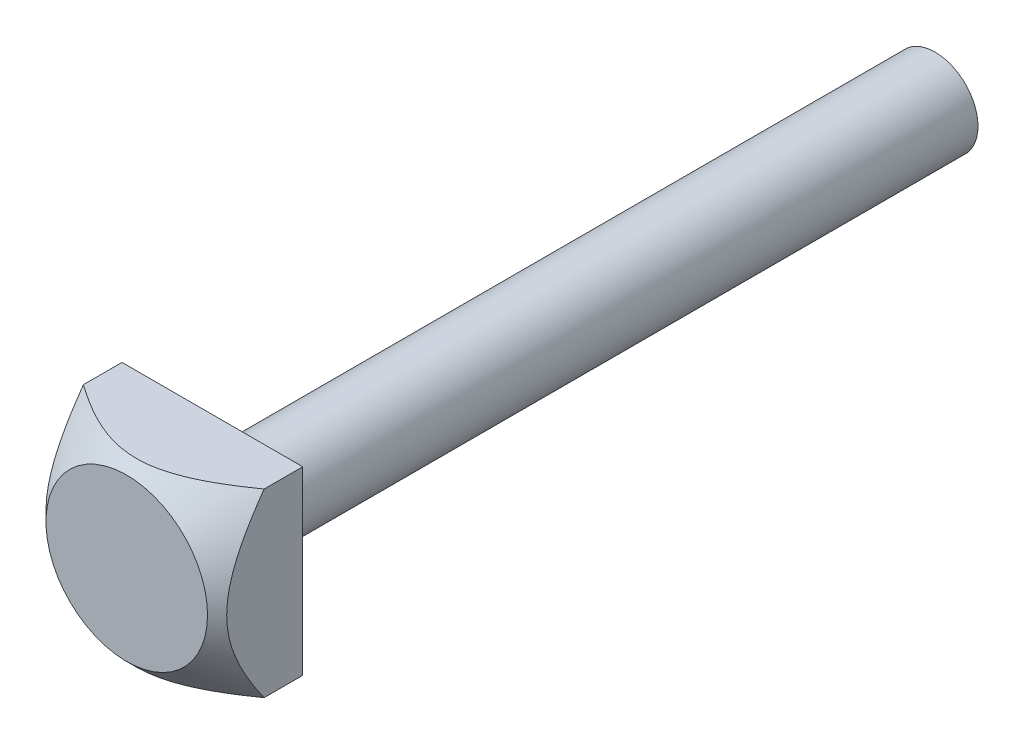
SolidWorks part; units mm, degrees
ref_plane "Front Plane" through (0, 0, 0) normal (0, 0, 1) x (1, 0, 0)
ref_plane "Top Plane" through (0, 0, 0) normal (0, 1, 0) x (1, 0, 0)
ref_plane "Right Plane" through (0, 0, 0) normal (1, 0, 0) x (0, 0, -1)
sketch "Sketch1" plane through (0, 0, 0) normal (0, 0, 1) x (1, 0, 0)
  line L1 (-9.5, 9.5) -> (9.5, 9.5)
  line L2 (-9.5, 9.5) -> (-9.5, -9.5)
  line L3 (-9.5, -9.5) -> (9.5, -9.5)
  line L4 (9.5, 9.5) -> (9.5, -9.5)
  line L5 (-9.5, 9.5) -> (9.5, -9.5) construction
  line L6 (-9.5, -9.5) -> (9.5, 9.5) construction
  point P0 (0, 0)
  dimension "D1" = 19
extrude "Boss-Extrude1" add sketch "Sketch1" along normal blind 9
sketch "Sketch2" plane through (0, 0, 9) normal (0, 0, 1) x (1, 0, 0)
  circle A0 centre (0, 0) radius 8.4929
extrude "Cut-Extrude1" cut sketch "Sketch2" against normal blind 9 draft 45 flip side to cut
sketch "Sketch3" plane through (0, 0, 0) normal (0, 0, -1) x (-1, 0, 0)
  circle A0 centre (0, 0) radius 4.5
  dimension "D1" = 9
extrude "Boss-Extrude2" add sketch "Sketch3" along normal blind 76
